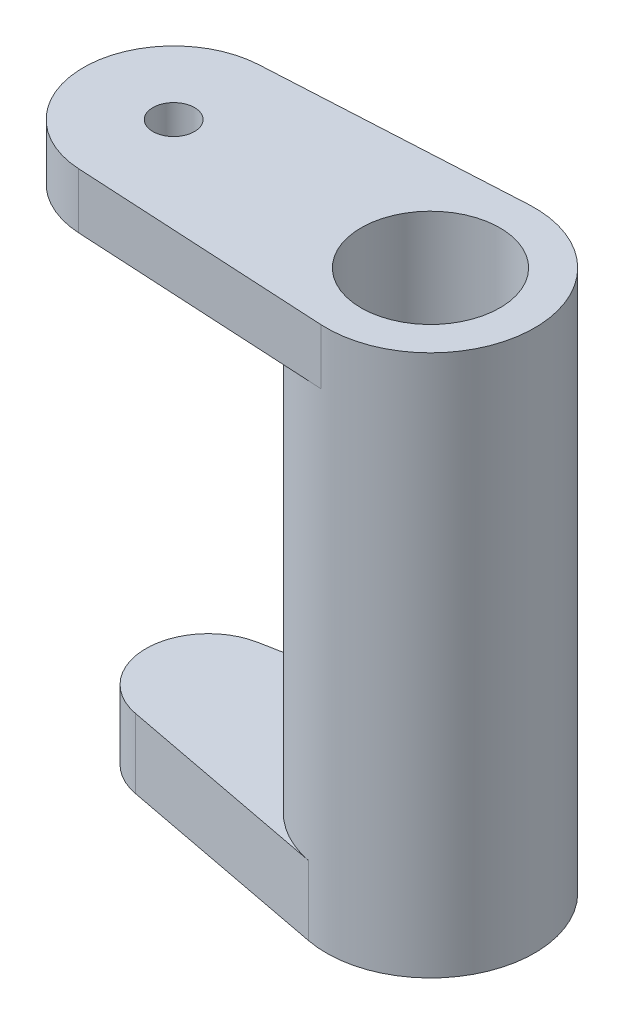
SolidWorks part; units mm, degrees
ref_plane "Alzado" through (0, 0, 0) normal (0, 0, 1) x (1, 0, 0)
ref_plane "Planta" through (0, 0, 0) normal (0, 1, 0) x (1, 0, 0)
ref_plane "Vista lateral" through (0, 0, 0) normal (1, 0, 0) x (0, 0, -1)
sketch "Croquis1" plane through (0, 0, 0) normal (0, 1, 0) x (1, 0, 0)
  circle A0 centre (-15.1843, -1.0325) radius 7.5
  dimension "D1" = 15
extrude "Saliente-Extruir1" add sketch "Croquis1" along normal blind 30
ref_plane "Plano1" through (0, 30, 0) normal (0, 1, 0) x (1, 0, 0)
sketch "Croquis2" plane through (0, 30, 0) normal (0, 1, 0) x (1, 0, 0)
  line L0 (-7.6843, -1.0325) -> (-40.1843, -1.0325) construction
  line L1 (-15.5897, -8.5216) -> (-34.0357, -7.523)
  line L2 (-15.5897, 6.4565) -> (-34.0357, 5.458)
  arc A0 (-15.5897, -8.5216) -> (-15.5897, 6.4565) centre (-15.1843, -1.0325) ccw
  arc A1 (-34.0357, 5.458) -> (-34.0357, -7.523) centre (-33.6843, -1.0325) ccw
  dimension "D1" = 32.5
  dimension "D2" = 13
  dimension "D3" = 15
extrude "Saliente-Extruir2" add sketch "Croquis2" along normal blind 4
ref_plane "Plano2" through (0, 0, 0) normal (0, -1, 0) x (-1, 0, 0)
sketch "Croquis3" plane through (0, 0, 0) normal (0, -1, 0) x (-1, 0, 0)
  line L0 (7.6843, -1.0325) -> (35.6843, -1.0325) construction
  line L1 (32.0281, -5.4527) -> (16.5906, -8.3995)
  line L2 (32.0281, 3.3877) -> (16.5906, 6.3345)
  arc A0 (16.5906, 6.3345) -> (16.5906, -8.3995) centre (15.1843, -1.0325) ccw
  arc A1 (32.0281, -5.4527) -> (32.0281, 3.3877) centre (31.1843, -1.0325) ccw
  dimension "D1" = 28
  dimension "D2" = 15
  dimension "D3" = 9
extrude "Saliente-Extruir3" add sketch "Croquis3" along normal blind 5
sketch "Croquis4" plane through (0, 34, 0) normal (0, 1, 0) x (1, 0, 0)
  circle A0 centre (-33.6843, -1.0325) radius 1.5
  arc A1 (-34.0357, 5.458) -> (-34.0357, -7.523) centre (-33.6843, -1.0325) ccw construction
  dimension "D1" = 3
extrude "Cortar-Extruir1" cut sketch "Croquis4" against normal blind 5
sketch "Croquis5" plane through (0, 34, 0) normal (0, 1, 0) x (1, 0, 0)
  circle A0 centre (-15.1843, -1.0325) radius 5
  dimension "D1" = 10
extrude "Cortar-Extruir2" cut sketch "Croquis5" against normal through all
